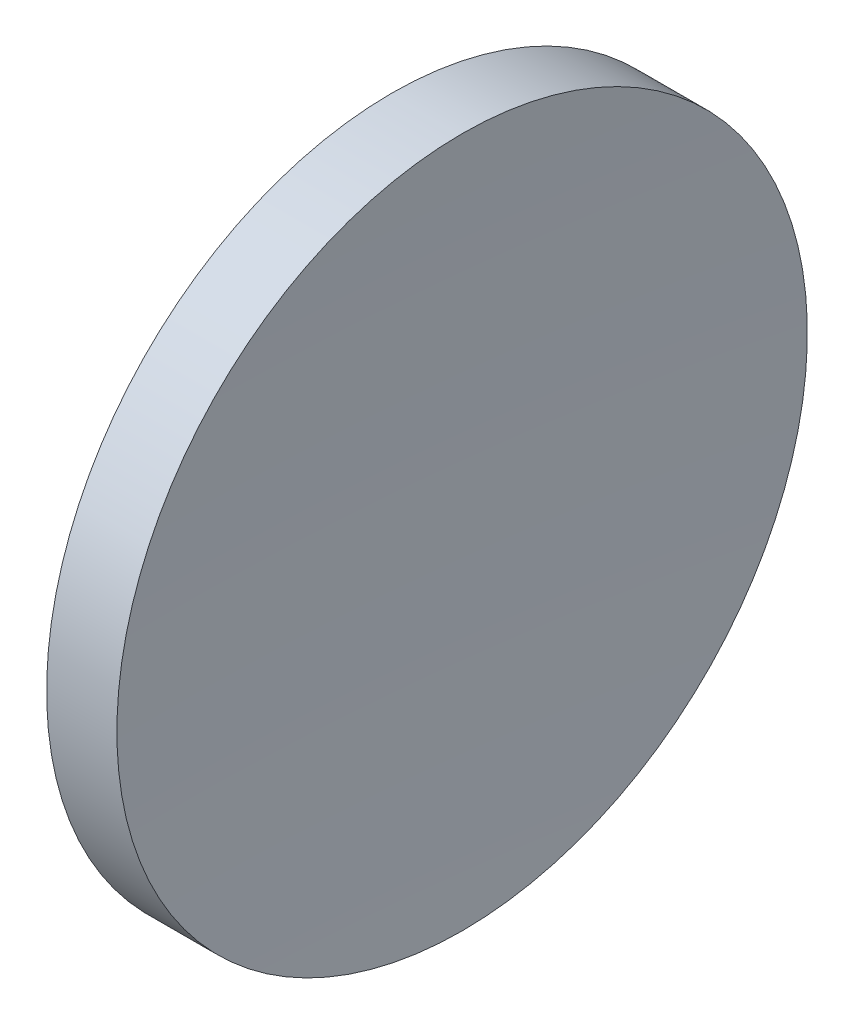
SolidWorks part; units mm, degrees
ref_plane "前视基准面" through (0, 0, 0) normal (0, 0, 1) x (1, 0, 0)
ref_plane "上视基准面" through (0, 0, 0) normal (0, 1, 0) x (1, 0, 0)
ref_plane "右视基准面" through (0, 0, 0) normal (1, 0, 0) x (0, 0, -1)
sketch "草图1" plane through (0, 0, 0) normal (0, 0, 1) x (1, 0, 0)
  line L0 (115.9445, 65.2168) -> (135.9482, 65.2168) construction
  line L1 (123.4944, 77.7168) -> (126.0379, 77.7168)
  line L2 (122.6122, 65.2168) -> (125.7122, 65.2168)
  arc A0 (123.4944, 77.7168) -> (122.6122, 65.2168) centre (211.6122, 65.2168) ccw
  arc A1 (126.0379, 77.7168) -> (125.7122, 65.2168) centre (365.7122, 65.2168) ccw
revolve "旋转1" add sketch "草图1" angle 360 about L0
